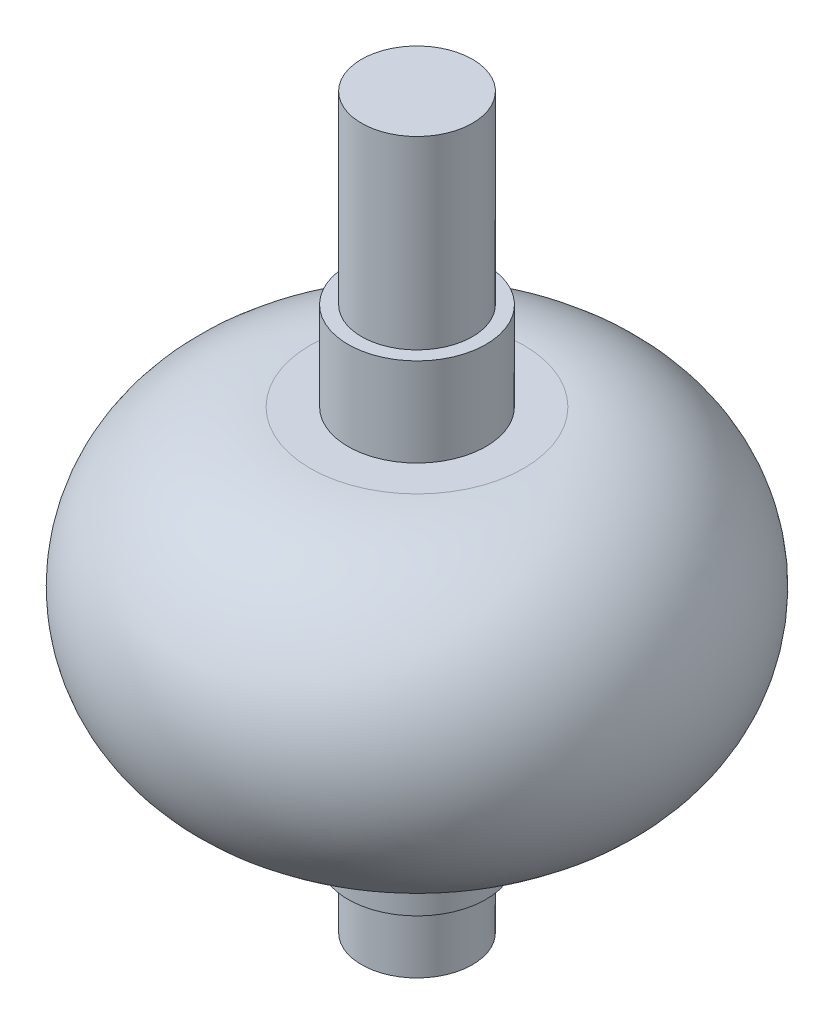
SolidWorks part; units mm, degrees
ref_plane "Front Plane" through (0, 0, 0) normal (0, 0, 1) x (1, 0, 0)
ref_plane "Top Plane" through (0, 0, 0) normal (0, 1, 0) x (1, 0, 0)
ref_plane "Right Plane" through (0, 0, 0) normal (1, 0, 0) x (0, 0, -1)
sketch "Эскиз1" plane through (0, 0, 0) normal (0, 0, 1) x (1, 0, 0)
  line L0 (0, 0) -> (0, 50) construction
  line L1 (0, 42.2213) -> (-3, 42.2213)
  line L2 (-3, 42.2213) -> (-3, 32.2213)
  line L3 (-3, 32.2213) -> (-3.7288, 32.2213)
  line L4 (-3.7288, 32.2213) -> (-3.7288, 27.4356)
  line L5 (-3.7288, 27.4356) -> (-5.7739, 27.4356)
  line L6 (-5.7739, 10.612) -> (-3.7288, 10.612)
  line L7 (-3.7288, 10.612) -> (-3.7288, 6.2185)
  line L8 (-3.7288, 6.2185) -> (-3, 6.2185)
  line L9 (-3, 6.2185) -> (-3, 2.7957)
  line L10 (-3, 2.7957) -> (0, 2.7957)
  line L11 (0, 42.2213) -> (0, 2.7957)
  arc A0 (-5.7739, 27.4356) -> (-5.7739, 10.612) centre (-5.7739, 19.0238) ccw
revolve "Повернуть1" add sketch "Эскиз1" angle 360 about L0
